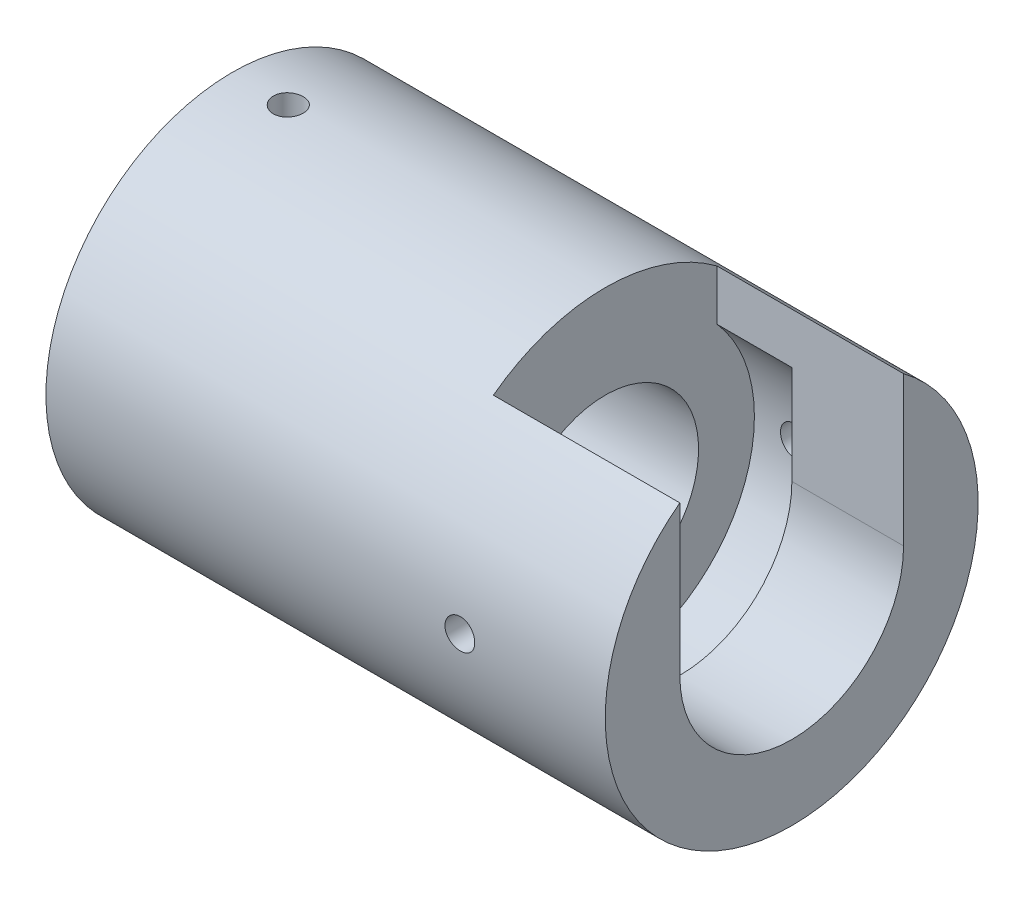
SolidWorks part; units mm, degrees
ref_plane "Front Plane" through (0, 0, 0) normal (0, 0, 1) x (1, 0, 0)
ref_plane "Top Plane" through (0, 0, 0) normal (0, 1, 0) x (1, 0, 0)
ref_plane "Right Plane" through (0, 0, 0) normal (1, 0, 0) x (0, 0, -1)
sketch "Sketch1" plane through (0, 0, 0) normal (1, 0, 0) x (0, 0, -1)
  circle A0 centre (0, 0) radius 10
  dimension "D1" = 20
extrude "Boss-Extrude1" add sketch "Sketch1" along normal blind 30
sketch "Sketch2" plane through (0, 0, 0) normal (-1, 0, 0) x (0, 0, 1)
  circle A0 centre (0, 0) radius 5.005
  dimension "D1" = 10.01
extrude "Cut-Extrude1" cut sketch "Sketch2" against normal blind 20
sketch "Sketch3" plane through (30, 0, 0) normal (1, 0, 0) x (0, 0, -1)
  line L0 (-6, 0) -> (-6, 8)
  line L1 (6, 0) -> (6, 8)
  arc A0 (-6, 0) -> (6, 0) centre (0, 0) ccw
  arc A2 (6, 8) -> (-6, 8) centre (0, 0) ccw
  dimension "D1" = 12
  dimension "D2" = 20
extrude "Cut-Extrude2" cut sketch "Sketch3" against normal up to surface (10 mm away) up to face at (20, 0, 5.005)
sketch "Sketch4" plane through (20, 0, 0) normal (1, 0, 0) x (0, 0, -1)
  circle A0 centre (0, 0) radius 8
  dimension "D1" = 16
extrude "Cut-Extrude3" cut sketch "Sketch4" along normal blind 4.01
ref_plane "Plane1" through (0, 0, -10) normal (0, 0, 1) x (1, 0, 0)
hole_wizard "M2x0.4 Tapped Hole1" positions "Sketch22" profile "Sketch23" tap size "M2x0.4" standard "ANSI Metric"
sketch "Sketch22" plane through (0, 0, -10) normal (0, 0, 1) x (1, 0, 0)
  line L0 (0, 0) -> (36.8629, 0) construction
  line L2 (30, -10) -> (30, 8) construction
  point P0 (22.2, 0)
  point P8 (0, 0)
  dimension "D1" = 7.8
sketch "Sketch23" plane through (22.2, 0, -10) normal (1, 0, 0) x (0, 1, 0)
  line L0 (0, 0) -> (0, 2)
  line L1 (0, 2) -> (0.8, 2)
  line L2 (0.8, 2) -> (0.8, 0)
  line L5 (0.8, 0) -> (0, 0)
  line L11 (0, -6.35) -> (0, 107.95) construction
  dimension "Thru Tap Drill Dia." = 1.6
  dimension "Thru Tap Drill Depth" = 2
cosmetic thread "Hole Thread5" parameters "D2"=2
ref_plane "Plane2" through (0, 0, 10) normal (0, 0, 1) x (1, 0, 0)
hole_wizard "M2x0.4 Tapped Hole2" positions "Sketch12" profile "Sketch13" tap size "M2x0.4" standard "ANSI Metric" end condition up to next
sketch "Sketch12" plane through (0, 0, 10) normal (0, 0, 1) x (1, 0, 0)
  line L0 (30, -10) -> (30, 8) construction
  line L2 (0, 0) -> (39.7675, 0) construction
  point P0 (22.2, 0)
  point P12 (0, 0)
  dimension "D1" = 7.8
sketch "Sketch13" plane through (22.2, 0, 10) normal (1, 0, 0) x (0, -1, 0)
  line L0 (0, 0) -> (0, 2)
  line L1 (0, 2) -> (0.8, 2)
  line L2 (0.8, 2) -> (0.8, 0)
  line L5 (0.8, 0) -> (0, 0)
  line L11 (0, -6.35) -> (0, 107.95) construction
  dimension "Thru Tap Drill Dia." = 1.6
  dimension "Thru Tap Drill Depth" = 2
cosmetic thread "Hole Thread2" parameters "D2"=2
ref_plane "Plane3" through (0, -10, 0) normal (0, 1, 0) x (1, 0, 0)
hole_wizard "M2x0.4 Tapped Hole3" positions "Sketch15" profile "Sketch16" tap size "M2x0.4" standard "ANSI Metric" end condition up to next
sketch "Sketch15" plane through (0, -10, 0) normal (0, 1, 0) x (1, 0, 0)
  line L0 (0, 0) -> (38.4111, 0) construction
  line L1 (30, -10) -> (30, 10) construction
  point P6 (22.2, 0)
  point P9 (0, 0)
  point P10 (0, 0)
  point P11 (0, 0)
  dimension "D1" = 7.8
sketch "Sketch16" plane through (22.2, -10, 0) normal (1, 0, 0) x (0, 0, -1)
  line L0 (0, 0) -> (0, 2)
  line L1 (0, 2) -> (0.8, 2)
  line L2 (0.8, 2) -> (0.8, 0)
  line L5 (0.8, 0) -> (0, 0)
  line L11 (0, -6.35) -> (0, 107.95) construction
  dimension "Thru Tap Drill Dia." = 1.6
  dimension "Thru Tap Drill Depth" = 2
cosmetic thread "Hole Thread3" parameters "D2"=2
ref_plane "Plane4" through (0, 10, 0) normal (0, 1, 0) x (1, 0, 0)
hole_wizard "M2x0.4 Tapped Hole4" positions "Sketch20" profile "Sketch21" tap size "M2x0.4" standard "ANSI Metric"
sketch "Sketch20" plane through (0, 10, 0) normal (0, 1, 0) x (1, 0, 0)
  line L0 (0, 0) -> (23.7994, 0) construction
  line L2 (0, 10) -> (0, -10) construction
  point P0 (3, 0)
  dimension "D1" = 3
sketch "Sketch21" plane through (3, 10, 0) normal (1, 0, 0) x (0, 0, 1)
  line L0 (0, 0) -> (0, 4.995)
  line L1 (0, 4.995) -> (0.8, 4.995)
  line L2 (0.8, 4.995) -> (0.8, 0)
  line L5 (0.8, 0) -> (0, 0)
  line L11 (0, -6.35) -> (0, 107.95) construction
  dimension "Thru Tap Drill Dia." = 1.6
  dimension "Thru Tap Drill Depth" = 4.995
cosmetic thread "Hole Thread4" parameters "D2"=2
